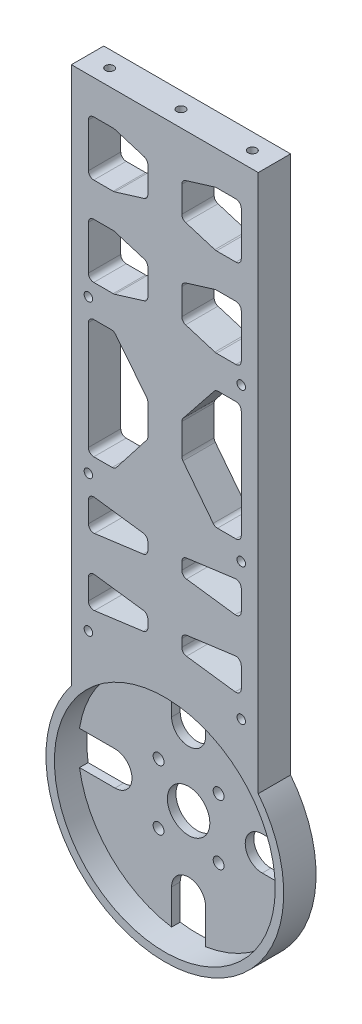
SolidWorks part; units mm, degrees
material "6061-T6 (SS)"
ref_plane "Front Plane" through (0, 0, 0) normal (0, 0, 1) x (1, 0, 0)
ref_plane "Top Plane" through (0, 0, 0) normal (0, 1, 0) x (1, 0, 0)
ref_plane "Right Plane" through (0, 0, 0) normal (1, 0, 0) x (0, 0, -1)
sketch "Sketch1" plane through (0, 0, 0) normal (0, 0, 1) x (1, 0, 0)
  line L0 (0, 0) -> (70.7107, 70.7107) construction
  line L1 (-27.5, 180) -> (27.5, 180)
  line L2 (-27.5, 180) -> (-27.5, 21.6506)
  line L3 (27.5, 180) -> (27.5, 21.6506)
  line L4 (-22.5, 78.3253) -> (-22.5, 123.3253) construction
  line L5 (22.5, 78.3253) -> (22.5, 123.3253) construction
  line L6 (0, 574.8892) -> (0, -128.8892) construction
  line L7 (0, 0) -> (100, 0) construction
  line L8 (0, 0) -> (-70.7107, -70.7107) construction
  line L9 (0, 0) -> (70.7107, -70.7107) construction
  line L10 (0, 0) -> (-70.7107, 70.7107) construction
  line L11 (0, 0) -> (-100, 0) construction
  line L12 (-102.0168, 11.5) -> (100, 11.5) construction
  line L13 (-22.5, 38.9711) -> (22.5, 38.9711) construction
  line L14 (-14.4846, 117.7272) -> (-5.346, 106.2595)
  line L15 (-5, 105.2701) -> (-5, 96.37)
  line L16 (-5.3344, 95.3954) -> (-14.2455, 83.9382)
  line L17 (-20.9125, 118.3253) -> (-15.7261, 118.3253)
  line L18 (-20.9125, 83.3253) -> (-15.4986, 83.3253)
  line L19 (-22.5, 116.7378) -> (-22.5, 84.9128)
  line L20 (-22.5, 168.3978) -> (-22.5, 155.4728)
  line L21 (-20.9125, 153.8853) -> (-15.1989, 153.8853)
  line L22 (-20.9125, 169.9853) -> (-15.1989, 169.9853)
  line L23 (-20.9125, 143.8853) -> (-15.1989, 143.8853)
  line L24 (-22.5, 142.2978) -> (-22.5, 129.3728)
  line L25 (-20.9125, 127.7853) -> (-15.1989, 127.7853)
  line L26 (-14.7341, 169.9158) -> (-6.1227, 167.2791)
  line L27 (-5, 165.7611) -> (-5, 158.1095)
  line L28 (-6.1227, 156.5916) -> (-14.7341, 153.9549)
  line L29 (-14.7341, 143.8158) -> (-6.1227, 141.1791)
  line L30 (-5, 139.6611) -> (-5, 132.0095)
  line L31 (-6.1227, 130.4916) -> (-14.7341, 127.8549)
  line L32 (-22.5, 71.5116) -> (-22.5, 65.462)
  line L33 (-22.5, 51.8345) -> (-22.5, 45.7849)
  line L34 (-20.7022, 73.0851) -> (-6.3772, 71.1708)
  line L35 (-5, 69.5973) -> (-5, 67.3762)
  line L36 (-6.3772, 65.8027) -> (-20.7022, 63.8885)
  line L37 (-20.7022, 53.408) -> (-6.3772, 51.4937)
  line L38 (-5, 49.9202) -> (-5, 47.6992)
  line L39 (-6.3772, 46.1256) -> (-20.7022, 44.2114)
  line L40 (6.3772, 46.1256) -> (20.7022, 44.2114)
  line L41 (5, 49.9202) -> (5, 47.6992)
  line L42 (20.7022, 53.408) -> (6.3772, 51.4937)
  line L43 (22.5, 71.5116) -> (22.5, 65.462)
  line L44 (20.7022, 63.8885) -> (6.3772, 65.8027)
  line L45 (5, 67.3762) -> (5, 69.5973)
  line L46 (22.5, 51.8345) -> (22.5, 45.7849)
  line L47 (6.3772, 71.1708) -> (20.7022, 73.0851)
  line L48 (6.1227, 130.4916) -> (14.7341, 127.8549)
  line L49 (5, 139.6611) -> (5, 132.0095)
  line L50 (14.7341, 143.8158) -> (6.1227, 141.1791)
  line L51 (6.1227, 156.5916) -> (14.7341, 153.9549)
  line L52 (5, 165.7611) -> (5, 158.1095)
  line L53 (14.7341, 169.9158) -> (6.1227, 167.2791)
  line L54 (20.9125, 127.7853) -> (15.1989, 127.7853)
  line L55 (22.5, 142.2978) -> (22.5, 129.3728)
  line L56 (20.9125, 143.8853) -> (15.1989, 143.8853)
  line L57 (20.9125, 169.9853) -> (15.1989, 169.9853)
  line L58 (20.9125, 153.8853) -> (15.1989, 153.8853)
  line L59 (22.5, 168.3978) -> (22.5, 155.4728)
  line L60 (22.5, 116.7378) -> (22.5, 84.9128)
  line L61 (20.9125, 83.3253) -> (15.4986, 83.3253)
  line L62 (20.9125, 118.3253) -> (15.7261, 118.3253)
  line L63 (5.3344, 95.3954) -> (14.2455, 83.9382)
  line L64 (5, 105.2701) -> (5, 96.37)
  line L65 (14.4846, 117.7272) -> (5.346, 106.2595)
  line L66 (5, 21.4665) -> (5, 32.1131)
  line L67 (-5, 21.4665) -> (-5, 32.1131)
  line L68 (21.67, 5) -> (32.1131, 5)
  line L69 (21.67, -5) -> (32.1131, -5)
  line L70 (5, -21.8722) -> (5, -32.1131)
  line L71 (-21.67, 5) -> (-32.1131, 5)
  line L72 (-21.67, -5) -> (-32.1131, -5)
  line L73 (-5, -21.8722) -> (-5, -32.1131)
  arc A0 (-27.5, 21.6506) -> (27.5, 21.6506) centre (0, 0) ccw
  arc A1 (22.5, 65.462) -> (20.7022, 63.8885) centre (20.9125, 65.462) cw
  arc A2 (22.5, 129.3728) -> (20.9125, 127.7853) centre (20.9125, 129.3728) cw
  arc A3 (15.1989, 127.7853) -> (14.7341, 127.8549) centre (15.1989, 129.3728) cw
  arc A4 (6.1227, 130.4916) -> (5, 132.0095) centre (6.5875, 132.0095) cw
  arc A5 (5, 139.6611) -> (6.1227, 141.1791) centre (6.5875, 139.6611) cw
  arc A6 (14.7341, 143.8158) -> (15.1989, 143.8853) centre (15.1989, 142.2978) cw
  arc A7 (20.9125, 143.8853) -> (22.5, 142.2978) centre (20.9125, 142.2978) cw
  arc A8 (22.5, 116.7378) -> (20.9125, 118.3253) centre (20.9125, 116.7378) ccw
  arc A9 (15.7261, 118.3253) -> (14.4846, 117.7272) centre (15.7261, 116.7378) ccw
  circle A10 centre (0, 0) radius 6.25
  arc A11 (-5, 21.4665) -> (5, 21.4665) centre (0, 21.4665) ccw
  arc A12 (21.67, 5) -> (21.67, -5) centre (21.67, 0) ccw
  arc A13 (5, -21.8722) -> (-5, -21.8722) centre (0, -21.8722) ccw
  arc A14 (-21.67, -5) -> (-21.67, 5) centre (-21.67, 0) ccw
  arc A15 (5.346, 106.2595) -> (5, 105.2701) centre (6.5875, 105.2701) ccw
  arc A16 (5, 96.37) -> (5.3344, 95.3954) centre (6.5875, 96.37) ccw
  arc A17 (14.2455, 83.9382) -> (15.4986, 83.3253) centre (15.4986, 84.9128) ccw
  arc A18 (20.9125, 83.3253) -> (22.5, 84.9128) centre (20.9125, 84.9128) ccw
  arc A19 (22.5, 71.5116) -> (20.7022, 73.0851) centre (20.9125, 71.5116) ccw
  arc A20 (5, 67.3762) -> (6.3772, 65.8027) centre (6.5875, 67.3762) ccw
  arc A21 (5, 69.5973) -> (6.3772, 71.1708) centre (6.5875, 69.5973) cw
  arc A23 (20.7022, 53.408) -> (22.5, 51.8345) centre (20.9125, 51.8345) cw
  arc A24 (22.5, 45.7849) -> (20.7022, 44.2114) centre (20.9125, 45.7849) cw
  arc A25 (6.3772, 46.1256) -> (5, 47.6992) centre (6.5875, 47.6992) cw
  arc A26 (5, 49.9202) -> (6.3772, 51.4937) centre (6.5875, 49.9202) cw
  arc A27 (-6.3772, 51.4937) -> (-5, 49.9202) centre (-6.5875, 49.9202) cw
  arc A28 (-5, 47.6992) -> (-6.3772, 46.1256) centre (-6.5875, 47.6992) cw
  arc A29 (-20.7022, 44.2114) -> (-22.5, 45.7849) centre (-20.9125, 45.7849) cw
  arc A30 (-22.5, 51.8345) -> (-20.7022, 53.408) centre (-20.9125, 51.8345) cw
  arc A31 (-5, 69.5973) -> (-6.3772, 71.1708) centre (-6.5875, 69.5973) ccw
  arc A32 (-5, 67.3762) -> (-6.3772, 65.8027) centre (-6.5875, 67.3762) cw
  arc A33 (-20.7022, 63.8885) -> (-22.5, 65.462) centre (-20.9125, 65.462) cw
  arc A34 (-22.5, 71.5116) -> (-20.7022, 73.0851) centre (-20.9125, 71.5116) cw
  arc A35 (-22.5, 84.9128) -> (-20.9125, 83.3253) centre (-20.9125, 84.9128) ccw
  arc A36 (-15.4986, 83.3253) -> (-14.2455, 83.9382) centre (-15.4986, 84.9128) ccw
  arc A37 (-5.3344, 95.3954) -> (-5, 96.37) centre (-6.5875, 96.37) ccw
  arc A38 (-5, 105.2701) -> (-5.346, 106.2595) centre (-6.5875, 105.2701) ccw
  arc A39 (-15.7261, 118.3253) -> (-14.4846, 117.7272) centre (-15.7261, 116.7378) cw
  arc A40 (-22.5, 116.7378) -> (-20.9125, 118.3253) centre (-20.9125, 116.7378) cw
  arc A41 (-20.9125, 143.8853) -> (-22.5, 142.2978) centre (-20.9125, 142.2978) ccw
  arc A42 (-22.5, 129.3728) -> (-20.9125, 127.7853) centre (-20.9125, 129.3728) ccw
  arc A43 (-15.1989, 127.7853) -> (-14.7341, 127.8549) centre (-15.1989, 129.3728) ccw
  arc A44 (-6.1227, 130.4916) -> (-5, 132.0095) centre (-6.5875, 132.0095) ccw
  arc A45 (-5, 139.6611) -> (-6.1227, 141.1791) centre (-6.5875, 139.6611) ccw
  arc A46 (-14.7341, 143.8158) -> (-15.1989, 143.8853) centre (-15.1989, 142.2978) ccw
  arc A47 (22.5, 155.4728) -> (20.9125, 153.8853) centre (20.9125, 155.4728) cw
  arc A48 (15.1989, 153.8853) -> (14.7341, 153.9549) centre (15.1989, 155.4728) cw
  arc A49 (6.1227, 156.5916) -> (5, 158.1095) centre (6.5875, 158.1095) cw
  arc A50 (5, 165.7611) -> (6.1227, 167.2791) centre (6.5875, 165.7611) cw
  arc A51 (14.7341, 169.9158) -> (15.1989, 169.9853) centre (15.1989, 168.3978) cw
  arc A52 (22.5, 168.3978) -> (20.9125, 169.9853) centre (20.9125, 168.3978) ccw
  arc A53 (-20.9125, 153.8853) -> (-22.5, 155.4728) centre (-20.9125, 155.4728) cw
  arc A54 (-15.1989, 153.8853) -> (-14.7341, 153.9549) centre (-15.1989, 155.4728) ccw
  arc A55 (-15.1989, 169.9853) -> (-14.7341, 169.9158) centre (-15.1989, 168.3978) cw
  arc A56 (-6.1227, 156.5916) -> (-5, 158.1095) centre (-6.5875, 158.1095) ccw
  arc A57 (-5, 165.7611) -> (-6.1227, 167.2791) centre (-6.5875, 165.7611) ccw
  arc A58 (-22.5, 168.3978) -> (-20.9125, 169.9853) centre (-20.9125, 168.3978) cw
  circle A70 centre (0, 0) radius 32.5
  point P1 (0, -35)
  point P2 (0, 180)
  point P8 (0, 11.5)
  point P11 (22.5, 127.7853)
  point P15 (14.9613, 127.7853)
  point P24 (-22.5, 100.8253)
  point P29 (22.5, 100.8253)
  point P35 (0, 180)
  point P48 (27.5, 100.8253)
  point P49 (-27.5, 100.8253)
  point P50 (22.5, 38.9711)
  point P53 (-22.5, 38.9711)
  point P60 (14.9613, 143.8853)
  point P64 (-22.5, 118.3253)
  point P69 (-22.5, 83.3253)
  point P81 (22.5, 143.8853)
  point P86 (22.5, 118.3253)
  point P94 (14.9613, 118.3253)
  point P110 (5, 105.8253)
  point P118 (5, 95.8253)
  point P126 (14.7222, 83.3253)
  point P129 (22.5, 83.3253)
  point P132 (22.5, 73.3253)
  point P133 (22.5, 63.6482)
  point P135 (5, 70.9868)
  point P137 (22.5, 73.3253)
  point P138 (5, 65.9868)
  point P141 (22.5, 63.6482)
  point P144 (22.5, 53.6482)
  point P147 (22.5, 43.9711)
  point P150 (5, 46.3097)
  point P153 (5, 51.3097)
  point P156 (-5, 51.3097)
  point P159 (-5, 46.3097)
  point P162 (-22.5, 43.9711)
  point P165 (-22.5, 53.6482)
  point P168 (-5, 70.9868)
  point P171 (-5, 65.9868)
  point P174 (-22.5, 63.6482)
  point P177 (-22.5, 73.3253)
  point P180 (-22.5, 83.3253)
  point P183 (-14.7222, 83.3253)
  point P186 (-5, 95.8253)
  point P189 (-5, 105.8253)
  point P192 (-14.9613, 118.3253)
  point P195 (-22.5, 118.3253)
  point P198 (-22.5, 143.8853)
  point P201 (-22.5, 127.7853)
  point P204 (-14.9613, 127.7853)
  point P211 (-14.9613, 143.8853)
  point P214 (22.5, 153.8853)
  point P217 (14.9613, 153.8853)
  point P220 (5, 156.9353)
  point P223 (5, 166.9353)
  point P226 (14.9613, 169.9853)
  point P229 (22.5, 169.9853)
  point P232 (-22.5, 153.8853)
  point P235 (-14.9613, 153.8853)
  point P238 (-14.9613, 169.9853)
  point P241 (-5, 156.9353)
  point P244 (-5, 166.9353)
  point P247 (-22.5, 169.9853)
  point P248 (-35, 0)
  point P249 (35, 0)
  point P251 (5, 65.9868)
  point P261 (5, 70.9868)
  dimension "D1" = 1.5875
  dimension "D3" = 70
  dimension "D2" = 215
  dimension "D8" = 1.5875
extrude "Boss-Extrude4" add sketch "Sketch1" along normal blind 9.525
sketch "Sketch3" plane through (0, 0, 9.525) normal (0, 0, 1) x (1, 0, 0)
  circle A0 centre (0, 0) radius 32.5
  dimension "D1" = 65
extrude "Cut-Extrude1" cut sketch "Sketch3" against normal blind 7
hole_wizard "Tap Drill for M3x0.5 Tap1" positions "Sketch9" profile "Sketch10" hole size "M3x0.5" standard "ANSI Metric"
sketch "Sketch9" plane through (0, 180, 0) normal (0, 1, 0) x (1, 0, 0)
  line L1 (27.5, -9.525) -> (27.5, 0) construction
  line L2 (-27.5, -4.7625) -> (27.5, -4.7625) construction
  line L3 (-27.5, -9.525) -> (-27.5, 0) construction
  line L5 (0, 0) -> (0, -9.525) construction
  line L6 (-27.5, 0) -> (27.5, 0) construction
  line L7 (-27.5, -9.525) -> (27.5, -9.525) construction
  point P0 (-21, -4.7625)
  point P2 (0, 16.8989)
  point P4 (21, -4.7625)
  point P29 (0, -4.7625)
  dimension "D1" = 6.5
  dimension "D2" = 6.5
sketch "Sketch10" plane through (-21, 180, 4.7625) normal (1, 0, 0) x (0, 0, 1)
  line L0 (0, 0) -> (0, 8.2511)
  line L1 (0, 8.2511) -> (1.25, 7.5)
  line L2 (1.25, 7.5) -> (1.25, 0)
  line L5 (1.25, 0) -> (0, 0)
  line L10 (0, 8.2511) -> (-1.25, 7.5) construction
  line L11 (0, -6.35) -> (0, 107.95) construction
  dimension "Hole Dia." = 2.5
  dimension "Hole Depth" = 7.5
  dimension "Drill Angle" = 118
hole_wizard "Tap Drill for M3x0.5 Tap2" positions "Sketch15" profile "Sketch14" hole size "M3x0.5" standard "ANSI Metric" end condition through all
sketch "Sketch15" plane through (0, 0, 9.525) normal (0, 0, 1) x (1, 0, 0)
  line L0 (-27.5, 180) -> (-27.5, 21.6506) construction
  line L1 (27.5, 180) -> (27.5, 21.6506) construction
  line L2 (-27.5, 100.8253) -> (27.5, 100.8253) construction
  point P0 (-22.5, 123.3253)
  point P2 (22.5, 123.3253)
  point P4 (22.5, 78.3253)
  point P6 (-22.5, 78.3253)
  dimension "D1" = 5
  dimension "D2" = 5
  dimension "D3" = 5
  dimension "D4" = 5
  dimension "D5" = 45
  dimension "D6" = 45
  dimension "D7" = 45
sketch "Sketch14" plane through (-22.5, 123.3253, 9.525) normal (1, 0, 0) x (0, -1, 0)
  line L0 (0, 0) -> (0, 9.525)
  line L1 (0, 9.525) -> (1.25, 9.525)
  line L2 (1.25, 9.525) -> (1.25, 0)
  line L5 (1.25, 0) -> (0, 0)
  line L11 (0, -6.35) -> (0, 107.95) construction
  dimension "Thru Hole Dia." = 2.5
  dimension "Thru Hole Depth" = 9.525
hole_wizard "Tap Drill for M3x0.5 Tap3" positions "Sketch17" profile "Sketch16" hole size "M3x0.5" standard "ANSI Metric" end condition through all
sketch "Sketch17" plane through (0, 0, 9.525) normal (0, 0, 1) x (1, 0, 0)
  line L0 (-27.5, 38.1393) -> (27.5, 38.1393) construction
  line L1 (-27.5, 180) -> (-27.5, 21.6506) construction
  line L2 (27.5, 180) -> (27.5, 21.6506) construction
  point P12 (-22.5, 38.1393)
  point P15 (22.5, 38.1393)
  dimension "D1" = 38.1393
  dimension "D3" = 5
  dimension "D4" = 5
  dimension "D5" = 45
sketch "Sketch16" plane through (-22.5, 38.1393, 9.525) normal (1, 0, 0) x (0, -1, 0)
  line L0 (0, 0) -> (0, 9.525)
  line L1 (0, 9.525) -> (1.25, 9.525)
  line L2 (1.25, 9.525) -> (1.25, 0)
  line L5 (1.25, 0) -> (0, 0)
  line L11 (0, -6.35) -> (0, 107.95) construction
  dimension "Thru Hole Dia." = 2.5
  dimension "Thru Hole Depth" = 9.525
hole_wizard "M3 Clearance Hole2" positions "Sketch21" profile "Sketch20" hole size "M3" standard "ANSI Metric" end condition through all
sketch "Sketch21" plane through (0, 0, 9.525) normal (0, 0, 1) x (1, 0, 0)
  line L0 (-21.67, 0) -> (23.0713, 0) construction
  line L2 (0, 0) -> (14.8165, 14.8165) construction
  line L4 (0, 0) -> (-15.8845, 15.8845) construction
  line L6 (0, 0) -> (16.0728, -16.0728) construction
  line L8 (0, 0) -> (-14.3263, -14.3263) construction
  circle A0 centre (0, 0) radius 6.25 construction
  point P0 (-8.8388, 8.8388)
  point P2 (8.8388, 8.8388)
  point P4 (8.8388, -8.8388)
  point P6 (-8.8388, -8.8388)
  dimension "D1" = 12.5
  dimension "D2" = 12.5
  dimension "D3" = 12.5
  dimension "D4" = 12.5
sketch "Sketch20" plane through (-8.8388, 8.8388, 9.525) normal (1, 0, 0) x (0, -1, 0)
  line L0 (0, 0) -> (0, 9.525)
  line L1 (0, 9.525) -> (1.6, 9.525)
  line L2 (1.6, 9.525) -> (1.6, 0)
  line L5 (1.6, 0) -> (0, 0)
  line L11 (0, -6.35) -> (0, 107.95) construction
  dimension "Thru Hole Dia." = 3.2
  dimension "Thru Hole Depth" = 9.525
